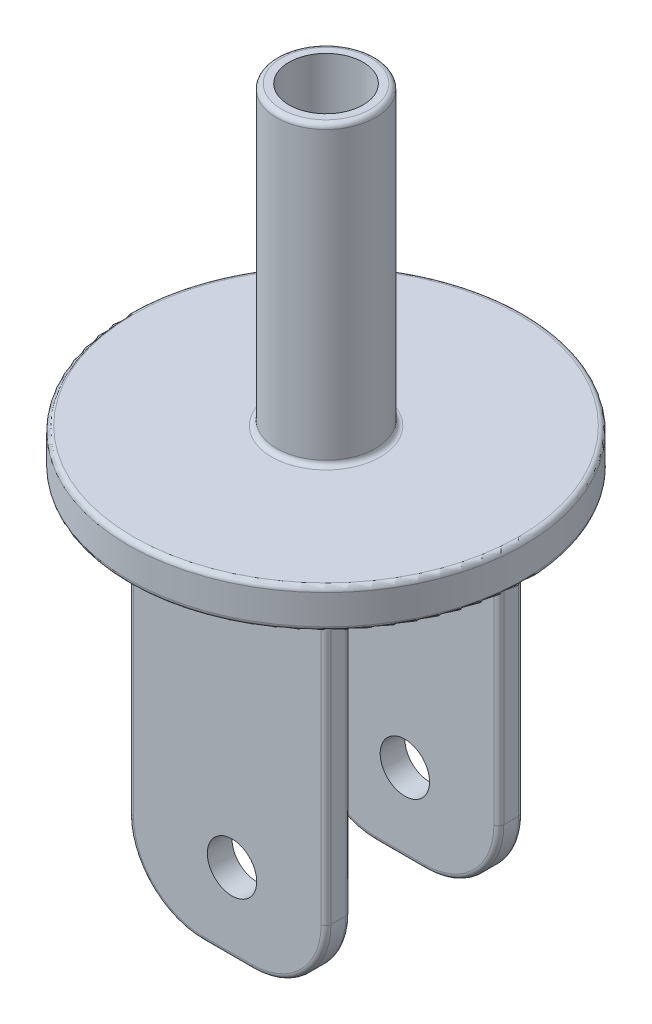
SolidWorks part; units mm, degrees
ref_plane "Front Plane" through (0, 0, 0) normal (0, 0, 1) x (1, 0, 0)
ref_plane "Top Plane" through (0, 0, 0) normal (0, 1, 0) x (1, 0, 0)
ref_plane "Right Plane" through (0, 0, 0) normal (1, 0, 0) x (0, 0, -1)
sketch "Sketch2" plane through (0, 0, 0) normal (0, 1, 0) x (1, 0, 0)
  circle A0 centre (0, 0) radius 40
  dimension "D1" = 80
extrude "Boss-Extrude1" add sketch "Sketch2" along normal blind 8
sketch "Sketch3" plane through (0, 0, 0) normal (0, -1, 0) x (1, 0, 0)
  line L0 (0, 0) -> (0, -17.5) construction
  line L2 (20, -20) -> (-20, -20)
  line L3 (20, -20) -> (20, -15)
  line L4 (20, -15) -> (-20, -15)
  line L5 (-20, -20) -> (-20, -15)
  line L6 (20, -20) -> (-20, -15) construction
  line L7 (20, -15) -> (-20, -20) construction
  point P7 (-20, -17.5)
  dimension "D1" = 15
  dimension "D2" = 40
  dimension "D3" = 2.5
extrude "Boss-Extrude2" add sketch "Sketch3" along normal blind 75
fillet "Fillet1" radius 15 2 edges at (20, -75, -17.5) (-20, -75, -17.5)
fillet "Fillet3" radius 1 10 edges at (20, -30, -20) (-20, -30, -20) (0, -75, -20) (15.6066, -70.6066, -20) (-15.6066, -70.6066, -20) (-20, -30, -15) (20, -30, -15) (15.6066, -70.6066, -15) (0, -75, -15) (-15.6066, -70.6066, -15)
fillet "Fillet4" radius 4 8 edges at (19.7071, 0, -15.2929) (20, 0, -17.5) (19.7071, 0, -19.7071) (0, 0, -20) (-19.7071, 0, -19.7071) (-20, 0, -17.5) (-19.7071, 0, -15.2929) (0, 0, -15)
mirror "Mirror10" about plane through (0, 0, 0) normal (0, 0, 1) of "Boss-Extrude2", "Fillet3", "Fillet1", "Fillet4"
sketch "Sketch5" plane through (0, 0, -20) normal (0, 0, -1) x (-1, 0, 0)
  line L0 (4.0384, -59) -> (-5.9616, -59) construction
  line L1 (-5, -74) -> (5, -74) construction
  circle A0 centre (-0.9616, -59) radius 5
  point P6 (0, -74)
  dimension "D2" = 10
  dimension "D1" = 10
  dimension "D3" = 15
extrude "Cut-Extrude1" cut sketch "Sketch5" against normal up to surface (40 mm away) contours A0 up to face at (0, -46.9665, 20)
sketch "Sketch6" plane through (0, 8, 0) normal (0, 1, 0) x (1, 0, 0)
  circle A0 centre (0, 0) radius 10
  dimension "D1" = 20
extrude "Boss-Extrude3" add sketch "Sketch6" along normal blind 60
sketch "Sketch7" plane through (0, 68, 0) normal (0, 1, 0) x (1, 0, 0)
  circle A0 centre (0, 0) radius 7.5
  dimension "D1" = 15
extrude "Cut-Extrude2" cut sketch "Sketch7" against normal blind 60
fillet "Fillet5" radius 1 4 edges at (0, 8, 40) (0, 8, 10) (0, 68, 10) (0, 0, 40)
sketch "Sketch8" plane through (0, 0, 0) normal (0, 0, 1) x (1, 0, 0)
  line L0 (0, 0) -> (-81.2112, 67) construction
  point P3 (-81.2112, 67)
ref_plane "Plane1" through (-81.2112, 67, 0) normal (-0.7714, 0.6364, 0) x (0, 0, 1)
